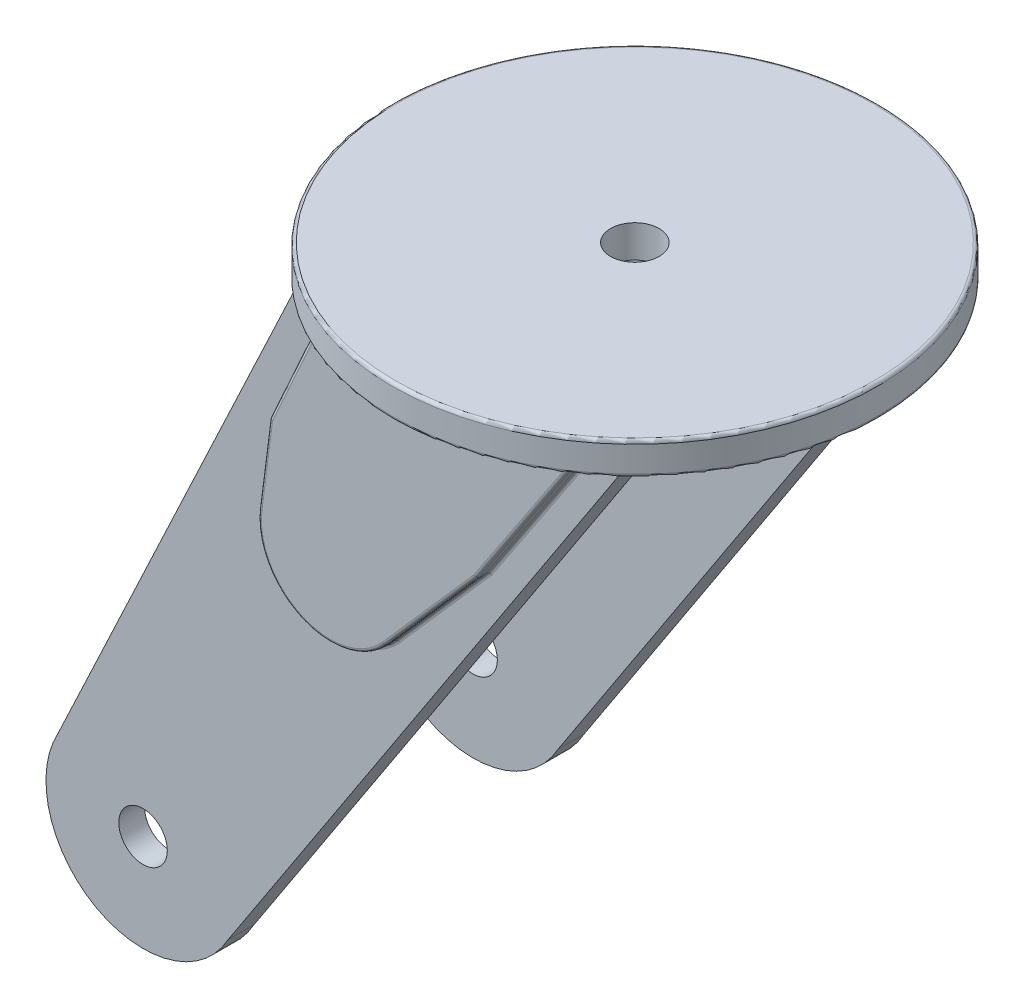
SolidWorks part; units mm, degrees
ref_plane "Front Plane" through (0, 0, 0) normal (0, 0, 1) x (1, 0, 0)
ref_plane "Top Plane" through (0, 0, 0) normal (0, 1, 0) x (1, 0, 0)
ref_plane "Right Plane" through (0, 0, 0) normal (1, 0, 0) x (0, 0, -1)
sketch "Sketch1" plane through (0, 0, 0) normal (0, 1, 0) x (1, 0, 0)
  circle A0 centre (0, 0) radius 75
  dimension "D1" = 150
extrude "Boss-Extrude1" add sketch "Sketch1" along normal blind 10
fillet "Fillet1" radius 1 2 edges at (0, 0, 75) (0, 10, 75)
ref_plane "Plane1" through (0, 0, 47) normal (0, 0, 1) x (1, 0, 0)
sketch "Sketch2" plane through (0, 0, 47) normal (0, 0, 1) x (1, 0, 0)
  line L0 (0, 0) -> (50, 0)
  line L1 (0, 0) -> (-50, 0)
  line L2 (-74, 0) -> (74, 0) construction
  line L3 (-50, 0) -> (-123.2436, -155.4648)
  line L4 (50, 0) -> (-70.7473, -184.5188)
  arc A0 (-123.2436, -155.4648) -> (-70.7473, -184.5188) centre (-97, -170) ccw
  circle A1 centre (-97, -170) radius 7.5
  dimension "D3" = 60
  dimension "D6" = 15
  dimension "D1" = 50
  dimension "D2" = 50
  dimension "D4" = 170
  dimension "D5" = 147
extrude "Boss-Extrude2" add sketch "Sketch2" along normal blind 8
sketch "Sketch4" plane through (0, 0, 55) normal (0, 0, 1) x (1, 0, 0)
  line L0 (40.2659, 0) -> (10.0128, -45.4804)
  line L2 (49.5076, 0) -> (-49.5076, 0) construction
  line L3 (10.0128, -45.4804) -> (-18.3249, -77.7)
  line L4 (40.2659, 0) -> (-38.3535, 0)
  line L5 (-38.3535, 0) -> (-53.9617, -34.4968)
  line L6 (-53.9617, -34.4968) -> (-57.2373, -60.1238)
  arc A0 (-57.2373, -60.1238) -> (-18.3249, -77.7) centre (-35.0903, -62.9546) ccw
extrude "Boss-Extrude3" add sketch "Sketch4" along normal blind 4
fillet "Fillet2" radius 1 10 edges at (25.1394, -22.7402, 55) (-4.156, -61.5902, 55) (-44.2811, -83.3024, 55) (-46.1576, -17.2484, 55) (-55.5995, -47.3103, 55) (25.1394, -22.7402, 59) (-4.156, -61.5902, 59) (-44.2811, -83.3024, 59) (-55.5995, -47.3103, 59) (-46.1576, -17.2484, 59)
sketch "Sketch6" plane through (0, 0, 47) normal (0, 0, -1) x (-1, 0, 0)
  line L0 (-40.2659, 0) -> (38.3535, 0)
  line L1 (-10.0128, -45.4804) -> (-40.2659, 0) construction
  line L2 (18.3249, -77.7) -> (-10.0128, -45.4804) construction
  line L3 (53.9617, -34.4968) -> (57.2373, -60.1238) construction
  line L4 (38.3535, 0) -> (53.9617, -34.4968) construction
  line L5 (38.3535, 0) -> (53.9617, -34.4968)
  line L6 (53.9617, -34.4968) -> (57.2373, -60.1238)
  line L7 (18.3249, -77.7) -> (-10.0128, -45.4804)
  line L8 (-10.0128, -45.4804) -> (-40.2659, 0)
  arc A0 (18.3249, -77.7) -> (57.2373, -60.1238) centre (35.0903, -62.9546) ccw construction
  arc A1 (18.3249, -77.7) -> (57.2373, -60.1238) centre (35.0903, -62.9546) ccw
extrude "Cut-Extrude1" cut sketch "Sketch6" against normal blind 4
fillet "Fillet3" radius 1 10 edges at (-46.1576, -17.2484, 51) (-46.1576, -17.2484, 47) (-55.5995, -47.3103, 47) (-55.5995, -47.3103, 51) (-44.2811, -83.3024, 47) (-44.2811, -83.3024, 51) (-4.156, -61.5902, 51) (-4.156, -61.5902, 47) (25.1394, -22.7402, 51) (25.1394, -22.7402, 47)
mirror "Mirror1" about plane through (0, 0, 0) normal (0, 0, 1) of "Boss-Extrude2", "Boss-Extrude3", "Cut-Extrude1", "Fillet2", "Fillet3"
sketch "Sketch7" plane through (0, 10, 0) normal (0, 1, 0) x (1, 0, 0)
  circle A0 centre (0, 0) radius 7.5
  dimension "D1" = 15
extrude "Cut-Extrude2" cut sketch "Sketch7" against normal through all
